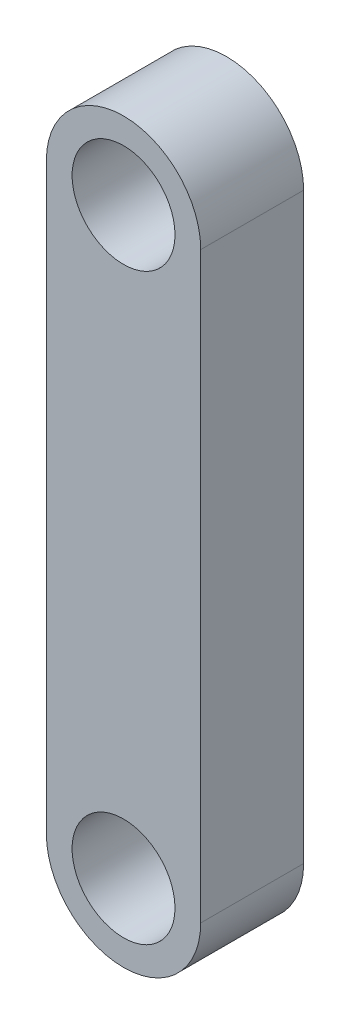
SolidWorks part; units mm, degrees
ref_plane "Front Plane" through (0, 0, 0) normal (0, 0, 1) x (1, 0, 0)
ref_plane "Top Plane" through (0, 0, 0) normal (0, 1, 0) x (1, 0, 0)
ref_plane "Right Plane" through (0, 0, 0) normal (1, 0, 0) x (0, 0, -1)
sketch "Model" plane through (0, 0, 0) normal (0, 0, 1) x (1, 0, 0)
  line L0 (67.75, 48.5) -> (67.75, 31.5)
  line L1 (72.25, 48.5) -> (72.25, 31.5)
  circle A0 centre (70, 48.5) radius 1.5
  circle A1 centre (70, 31.5) radius 1.5
  arc A2 (72.25, 48.5) -> (67.75, 48.5) centre (70, 48.5) ccw
  arc A3 (67.75, 31.5) -> (72.25, 31.5) centre (70, 31.5) ccw
extrude "Boss-Extrude1" add sketch "Model" along normal blind 3
